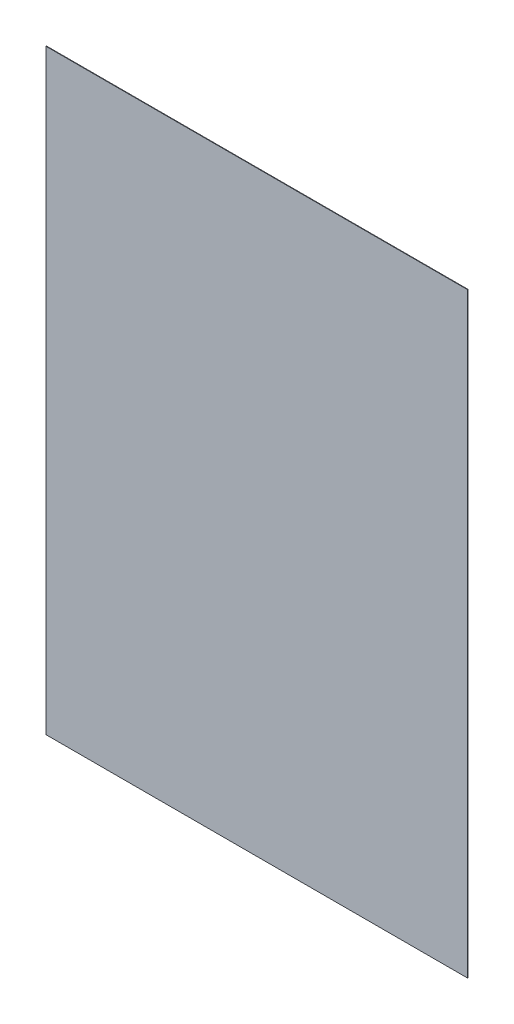
SolidWorks part; units mm, degrees
ref_plane "Front Plane" through (0, 0, 0) normal (0, 0, 1) x (1, 0, 0)
ref_plane "Top Plane" through (0, 0, 0) normal (0, 1, 0) x (1, 0, 0)
ref_plane "Right Plane" through (0, 0, 0) normal (1, 0, 0) x (0, 0, -1)
sketch "Sketch1" plane through (0, 0, 0) normal (0, 0, 1) x (1, 0, 0)
  line L1 (0, 0) -> (210.058, 0)
  line L2 (0, 0) -> (0, 297.18)
  line L3 (0, 297.18) -> (210.058, 297.18)
  line L4 (210.058, 0) -> (210.058, 297.18)
  dimension "D1" = 210.058
  dimension "D2" = 297.18
extrude "Boss-Extrude1" add sketch "Sketch1" along normal blind 0.254
